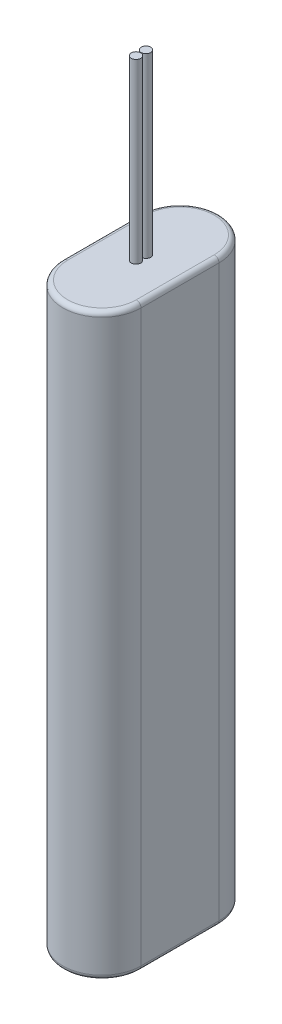
SolidWorks part; units mm, degrees
ref_plane "Face" through (0, 0, 0) normal (0, 0, 1) x (1, 0, 0)
ref_plane "Dessus" through (0, 0, 0) normal (0, 1, 0) x (1, 0, 0)
ref_plane "Droite" through (0, 0, 0) normal (1, 0, 0) x (0, 0, -1)
sketch "Esquisse1" plane through (0, 0, 0) normal (0, 1, 0) x (1, 0, 0)
  line L0 (0, 0) -> (0, 33)
  line L1 (33, 33) -> (33, 0)
  arc A0 (0, 33) -> (33, 33) centre (16.5, 33) cw
  arc A1 (0, 0) -> (33, 0) centre (16.5, 0) ccw
  dimension "D1" = 33
  dimension "D2" = 33
extrude "Extrusion1" add sketch "Esquisse1" along normal blind 245
fillet "Congé1" radius 2 8 edges at (16.5, 0, 16.5) (0, 0, -16.5) (33, 0, -16.5) (16.5, 0, -49.5) (16.5, 245, -49.5) (0, 245, -16.5) (16.5, 245, 16.5) (33, 245, -16.5)
sketch "Esquisse2" plane through (0, 245, 0) normal (0, 1, 0) x (1, 0, 0)
  line L0 (31, 16.5) -> (2, 16.5) construction
  line L1 (31, 0) -> (31, 33) construction
  line L2 (2, 33) -> (2, 0) construction
  line L3 (16.5, 47.5) -> (16.5, -14.5) construction
  arc A0 (31, 33) -> (2, 33) centre (16.5, 33) ccw construction
  arc A1 (2, 0) -> (31, 0) centre (16.5, 0) ccw construction
  circle A2 centre (16.5, 18.6) radius 2
  circle A3 centre (16.5, 14.4) radius 2
  dimension "D1" = 4
  dimension "D2" = 2.1
extrude "Extrusion2" add sketch "Esquisse2" along normal blind 75
